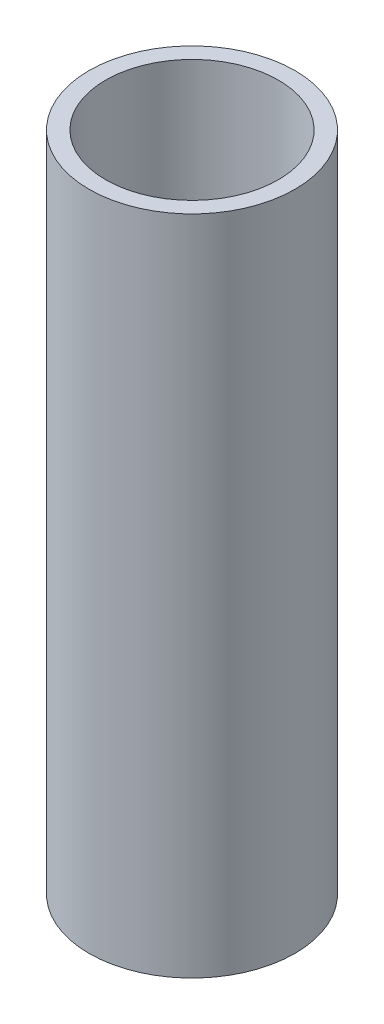
SolidWorks part; units mm, degrees
ref_plane "Front Plane" through (0, 0, 0) normal (0, 0, 1) x (1, 0, 0)
ref_plane "Top Plane" through (0, 0, 0) normal (0, 1, 0) x (1, 0, 0)
ref_plane "Right Plane" through (0, 0, 0) normal (1, 0, 0) x (0, 0, -1)
sketch "Sketch1" plane through (0, 0, 0) normal (0, 1, 0) x (1, 0, 0)
  circle A0 centre (0, 0) radius 23.6982
  dimension "D1" = 47.3964
extrude "Boss-Extrude1" add sketch "Sketch1" along normal blind 152.4
sketch "Sketch2" plane through (0, 152.4, 0) normal (0, 1, 0) x (1, 0, 0)
  circle A2 centre (0, 0) radius 19.8882
  circle A3 centre (0, 0) radius 19.8882
  dimension "D1" = 3.81
extrude "Cut-Extrude1" cut sketch "Sketch2" against normal up to next
